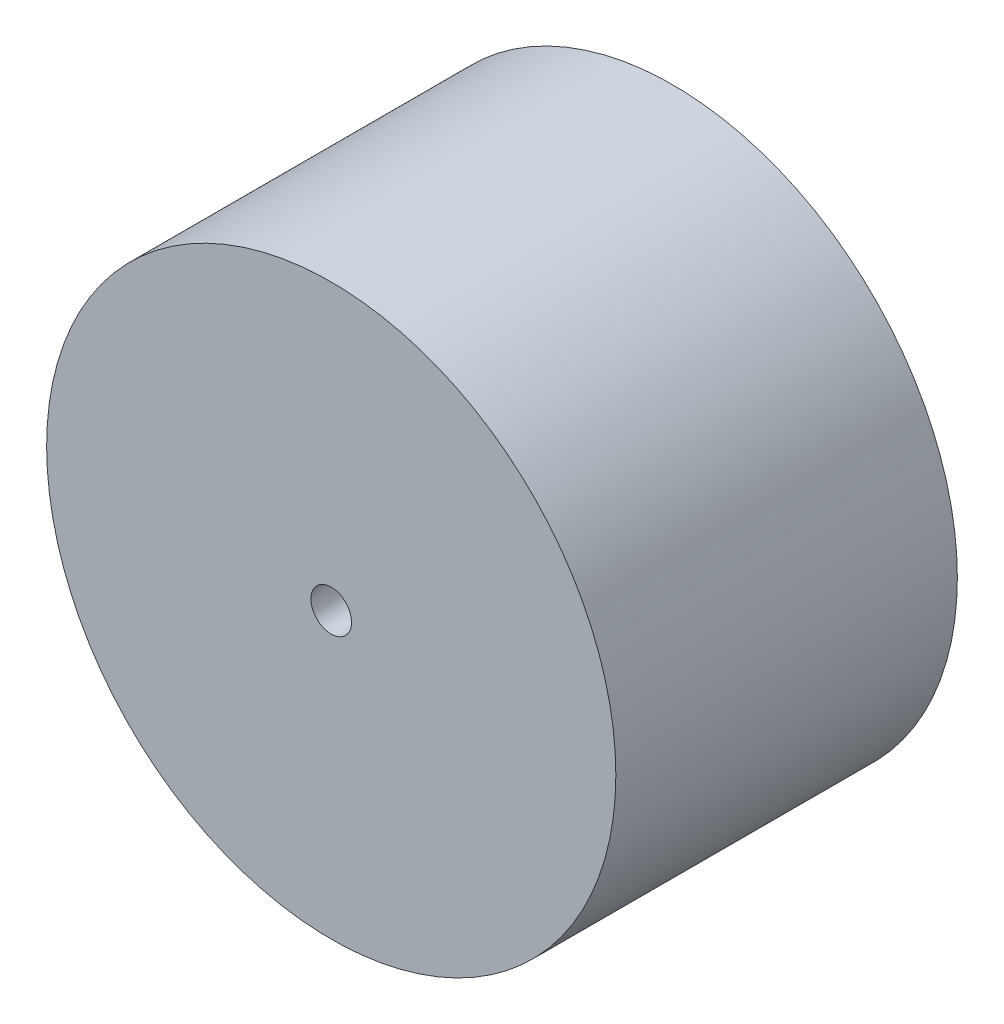
SolidWorks part; units mm, degrees
ref_plane "Front Plane" through (0, 0, 0) normal (0, 0, 1) x (1, 0, 0)
ref_plane "Top Plane" through (0, 0, 0) normal (0, 1, 0) x (1, 0, 0)
ref_plane "Right Plane" through (0, 0, 0) normal (1, 0, 0) x (0, 0, -1)
sketch "Sketch1" plane through (0, 0, 0) normal (0, 0, 1) x (1, 0, 0)
  circle A0 centre (0, 0) radius 35
  circle A1 centre (0, 0) radius 2.5
  dimension "D1" = 70
  dimension "D2" = 5
extrude "Boss-Extrude1" add sketch "Sketch1" along normal blind 42
